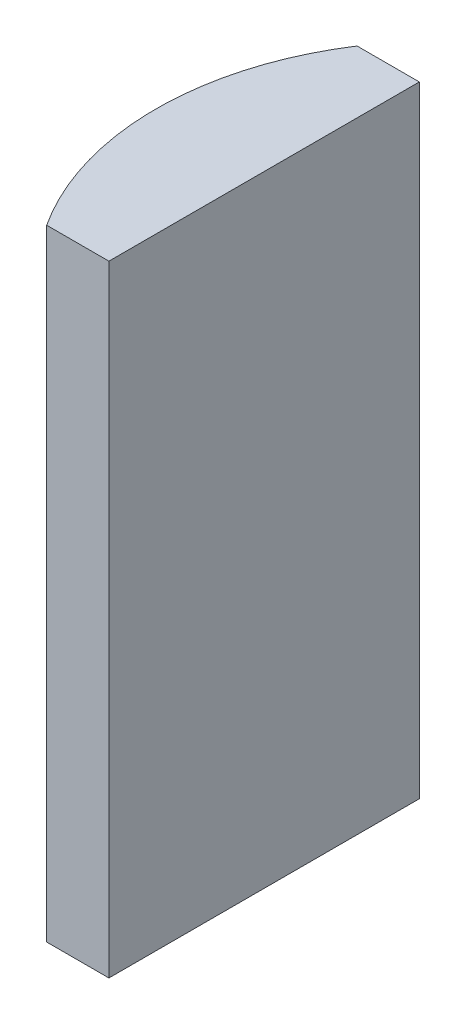
SolidWorks part; units mm, degrees
ref_plane "前视基准面" through (0, 0, 0) normal (0, 0, 1) x (1, 0, 0)
ref_plane "上视基准面" through (0, 0, 0) normal (0, 1, 0) x (1, 0, 0)
ref_plane "右视基准面" through (0, 0, 0) normal (1, 0, 0) x (0, 0, -1)
sketch "草图1" plane through (0, 0, 0) normal (0, 1, 0) x (1, 0, 0)
  line L0 (-137.6835, 0) -> (10.8051, 0) construction
  line L1 (-3.3198, 5) -> (-1.3148, 5)
  line L2 (-3.3198, -5) -> (-1.3148, -5)
  line L3 (-1.3148, 5) -> (-1.3148, -5)
  arc A0 (-3.3198, 5) -> (-3.3198, -5) centre (4.3552, 0) ccw
  point P2 (-4.8048, 0)
  point P4 (-1.3148, 0)
  dimension "D2" = 5
  dimension "D3" = 9.16
  dimension "D4" = 3.49
  dimension "D1" = 5
extrude "凸台-拉伸1" add sketch "草图1" along normal blind 20
